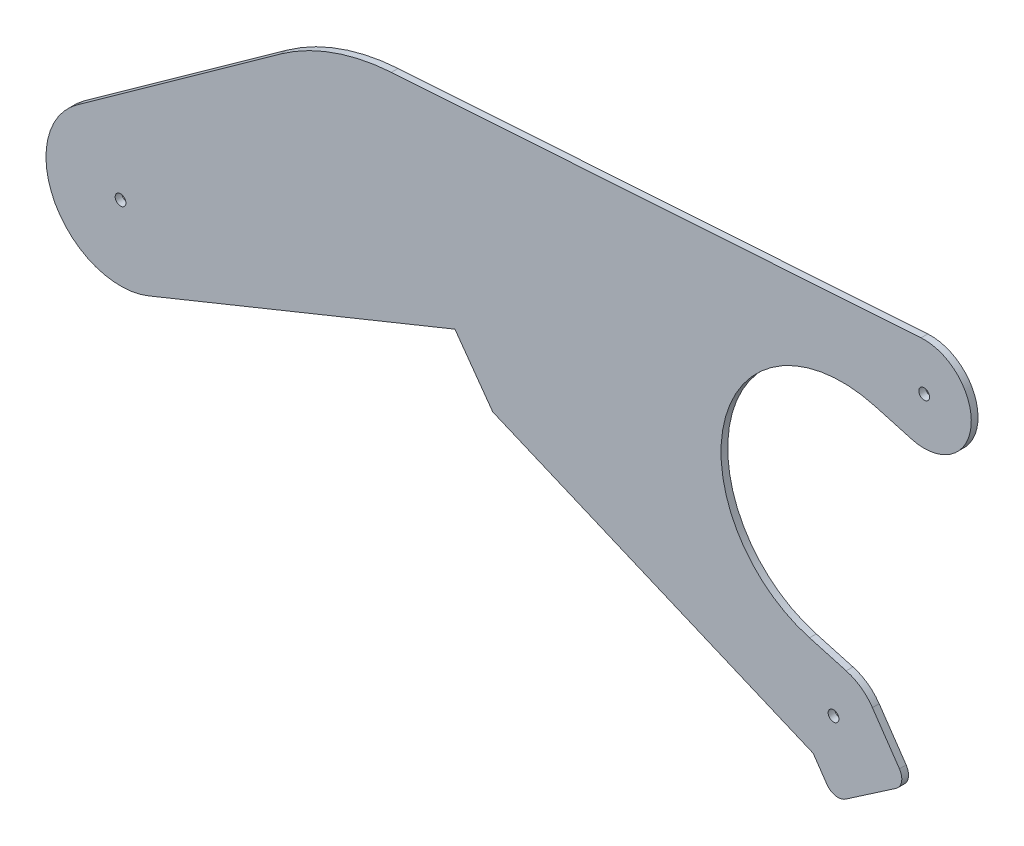
SolidWorks part; units mm, degrees
material "ABS PC"
ref_plane "Front Plane" through (0, 0, 0) normal (0, 0, 1) x (1, 0, 0)
ref_plane "Top Plane" through (0, 0, 0) normal (0, 1, 0) x (1, 0, 0)
ref_plane "Right Plane" through (0, 0, 0) normal (1, 0, 0) x (0, 0, -1)
sketch "Sketch1" plane through (0, 0, 0) normal (0, 0, 1) x (1, 0, 0)
  line L0 (0, 0) -> (0, 254) construction
  line L1 (133.35, 0) -> (133.35, 171.45) construction
  line L2 (0.0421, 0) -> (133.3921, 0) construction
  line L3 (50.8, 0) -> (50.8, 123.825) construction
  line L4 (508, 0) -> (508, 50000) construction
  line L11 (133.35, 171.45) -> (0, 171.45) construction
  line L20 (508, 457.2) -> (482.6, 457.2) construction
  line L22 (-203.2, 0) -> (-203.2, 53.1862) construction
  line L31 (-203.2, 558.8) -> (50.8, 558.8) construction
  line L48 (379.0299, 364.2668) -> (336.2871, 211.3792) construction
  line L49 (311.0917, 197.8988) -> (326.7032, 191.3013)
  line L50 (-20.4892, 282.5857) -> (75.2027, 351.1742)
  line L51 (127.7101, 369.9758) -> (377.5682, 386.4437)
  line L52 (13.2266, 221.4116) -> (97.7927, 255.7344)
  line L53 (175.5519, 255.1789) -> (311.0917, 197.8988)
  line L54 (342.2711, 232.7835) -> (324.9738, 237.6193)
  line L55 (355.7486, 347.6983) -> (373.0459, 342.8625)
  line L56 (326.7032, 191.3013) -> (333.1515, 181.877)
  line L57 (341.9779, 180.2221) -> (365.7239, 196.4695)
  line L58 (367.3788, 205.2959) -> (354.6295, 223.9294)
  line L59 (97.7927, 255.7344) -> (157.7202, 280.0571)
  line L60 (157.7202, 280.0571) -> (175.5519, 255.1789)
  line L61 (336.2871, 211.3792) -> (354.6295, 223.9294) construction
  circle A11 centre (508, 57.15) radius 57.15 construction
  circle A17 centre (379.0299, 364.2668) radius 28.575 construction
  circle A18 centre (336.2871, 211.3792) radius 28.575 construction
  arc A19 (-20.4892, 282.5857) -> (13.2266, 221.4116) centre (0, 254) ccw
  arc A20 (354.6295, 223.9294) -> (342.2711, 232.7835) centre (336.2871, 211.3792) ccw
  arc A21 (373.0459, 342.8625) -> (377.5682, 386.4437) centre (379.0299, 364.2668) ccw
  arc A22 (324.9738, 237.6193) -> (355.7486, 347.6983) centre (340.3612, 292.6588) cw
  circle A23 centre (379.0299, 364.2668) radius 2.54
  circle A24 centre (336.2871, 211.3792) radius 2.54
  circle A25 centre (0, 254) radius 2.54
  arc A26 (365.7239, 196.4695) -> (367.3788, 205.2959) centre (362.1381, 201.7102) ccw
  arc A27 (333.1515, 181.877) -> (341.9779, 180.2221) centre (338.3921, 185.4627) ccw
  arc A28 (75.2027, 351.1742) -> (127.7101, 369.9758) centre (134.3919, 268.5957) cw
  point P17 (-177.8, 889)
  point P19 (253.4719, 28.9276)
  point P24 (343.9808, 238.899)
  point P27 (340.6825, 179.3357)
  point P29 (270.4972, 43.2136)
  point P38 (98.7731, 368.0686)
  point P42 (136.7873, 271.5611)
  point P43 (0, 0)
  point P48 (0, 0)
  point P49 (0, 0)
  point P51 (0, 0)
  point P52 (0, 0)
  point P55 (280.3675, 35.2368)
  point P56 (391.5955, 204.2466)
  point P57 (399.6735, 254)
  point P58 (392.218, 310.9796)
  point P59 (387.1164, 332.9704)
  point P60 (127.7101, 368.0686)
  point P71 (342.613, 234.0066)
  dimension "D4" = 304.8
  dimension "D9" = 57.15
  dimension "D10" = 133.35
  dimension "D12" = 5.08
  dimension "D13" = 114.3
  dimension "D14" = 22.225
  dimension "D21" = 114.3
  dimension "D3" = 171.45
  dimension "D6" = 57.15
  dimension "D15" = 22.225
  dimension "D25" = 64.6753
  dimension "D23" = 189.2304
  dimension "D8" = 69.85
  dimension "D16" = 114.3
  dimension "D22" = 279.4
  dimension "D28" = 5.08
  dimension "D29" = 6.35
  dimension "D30" = 101.6
  dimension "D1" = 82.55
  dimension "D2" = 254
  dimension "D5" = 50.8
  dimension "D7" = 457.2
  dimension "D17" = 457.2
  dimension "D18" = 177.8
  dimension "D19" = 889
  dimension "D20" = 25.4
  dimension "D24" = 135
  dimension "4.5" = 203.2
  dimension "D26" = 41.4724
  dimension "D27" = 18.401
  dimension "D31" = 30.6088
  dimension "D32" = 103.541
  dimension "D33" = 13.541
  dimension "D34" = 11.4191
  dimension "D35" = 22.5776
  dimension "D36" = 40
  dimension "D37" = 147.29
  dimension "D38" = 140
  dimension "D39" = 148.139
extrude "Boss-Extrude1" add sketch "Sketch1" along normal blind 3.175
